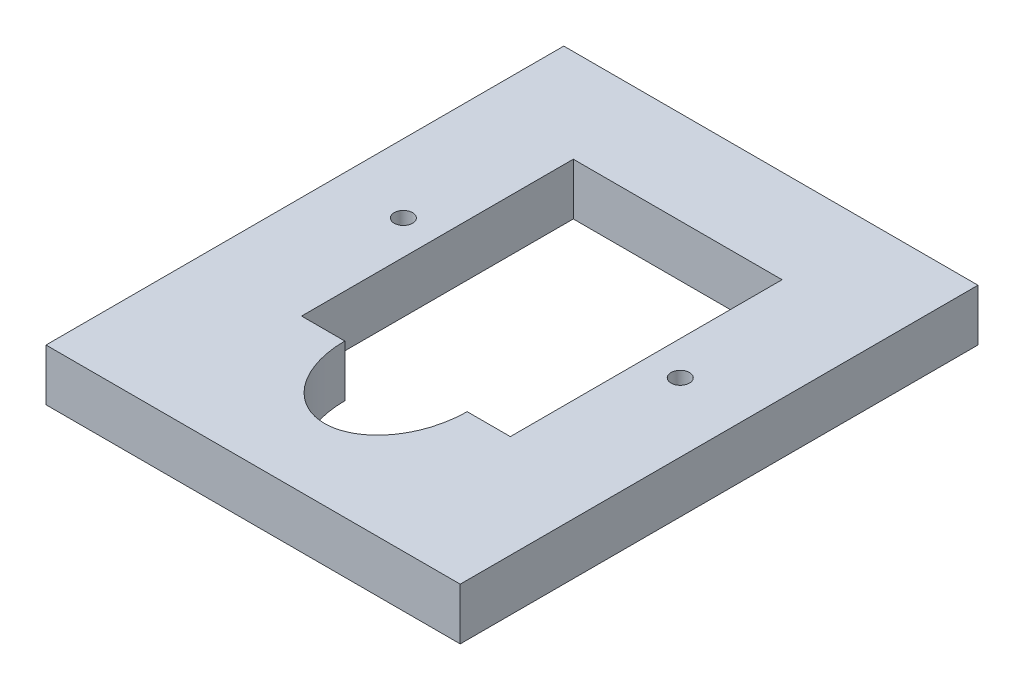
SolidWorks part; units mm, degrees
ref_plane "Front Plane" through (0, 0, 0) normal (0, 0, 1) x (1, 0, 0)
ref_plane "Top Plane" through (0, 0, 0) normal (0, 1, 0) x (1, 0, 0)
ref_plane "Right Plane" through (0, 0, 0) normal (1, 0, 0) x (0, 0, -1)
sketch "Sketch1" plane through (0, 0, 0) normal (0, 1, 0) x (1, 0, 0)
  line L0 (21.7665, 29.8808) -> (21.7665, -33.6192) construction
  line L1 (-3.6335, 29.8808) -> (47.1665, 29.8808)
  line L2 (-3.6335, 29.8808) -> (-3.6335, -33.6192)
  line L3 (-3.6335, -33.6192) -> (47.1665, -33.6192)
  line L4 (47.1665, 29.8808) -> (47.1665, -33.6192)
  line L5 (29.2665, -14.874) -> (34.5681, -14.874)
  line L6 (8.9649, 18.4508) -> (34.5681, 18.4508)
  line L7 (8.9649, 18.4508) -> (8.9649, -14.874)
  line L8 (8.9649, -14.874) -> (14.2665, -14.874)
  line L9 (34.5681, 18.4508) -> (34.5681, -14.874)
  circle A0 centre (38.7439, 1.7884) radius 1.1303
  circle A1 centre (4.7892, 1.7884) radius 1.1303
  ellipse E0 centre (21.7665, -14.874) end of major axis (21.7665, -4.874) minor radius 7.5 (14.2665, -14.874) -> (29.2665, -14.874) ccw
  dimension "D11" = 2.2606
  dimension "D12" = 2.2606
  dimension "D13" = 10
  dimension "D1" = 50.8
  dimension "D2" = 63.5
  dimension "D3" = 33.3248
  dimension "D4" = 25.6032
  dimension "D5" = 11.43
  dimension "D6" = 12.8016
  dimension "D7" = 4.1758
  dimension "D8" = 4.1758
  dimension "D9" = 16.6624
  dimension "D10" = 16.6624
  dimension "D14" = 7.5
extrude "Boss-Extrude1" add sketch "Sketch1" along normal blind 6.35
